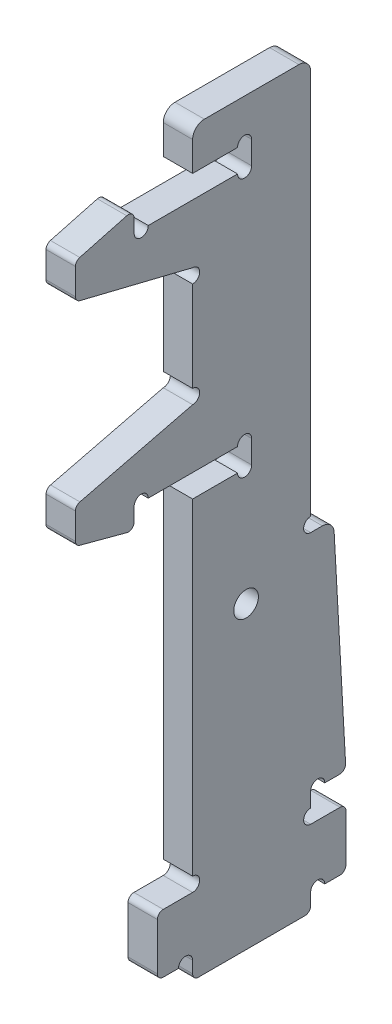
SolidWorks part; units mm, degrees
ref_plane "前视基准面" through (0, 0, 0) normal (0, 0, 1) x (1, 0, 0)
ref_plane "上视基准面" through (0, 0, 0) normal (0, 1, 0) x (1, 0, 0)
ref_plane "右视基准面" through (0, 0, 0) normal (1, 0, 0) x (0, 0, -1)
sketch "草图2" plane through (0, 0, 0) normal (1, 0, 0) x (0, 0, -1)
  line L0 (-5.025, 65) -> (-5.025, 8.5)
  line L1 (-5.025, 8.5) -> (-8.025, 8.5)
  line L2 (-8.025, 8.5) -> (-8.025, 3.5)
  line L3 (-8.025, 3.5) -> (-5.025, 3.5)
  line L4 (-5.025, 3.5) -> (-5.025, 2)
  line L5 (-5.025, 2) -> (5.025, 2)
  line L6 (5.025, 2) -> (5.025, 3.5)
  line L7 (5.025, 3.5) -> (8.025, 3.5)
  line L8 (8.025, 3.5) -> (8.025, 8.5)
  line L9 (8.025, 8.5) -> (5.025, 8.5)
  line L10 (5.025, 8.5) -> (5.025, 65)
  line L11 (5.025, 65) -> (-5.025, 65)
  line L12 (5.025, 0) -> (-5.025, 0) construction
  point P13 (-8.025, 6)
  point P19 (0, 0)
  dimension "D1" = 3
  dimension "D2" = 5
  dimension "D3" = 10.05
  dimension "D4" = 1.5
  dimension "D5" = 130
  dimension "D6" = 6
extrude "凸台-拉伸1" add sketch "草图2" along normal mid plane 2.5
sketch "草图4" plane through (-1.25, 0, 0) normal (-1, 0, 0) x (0, 0, 1)
  line L0 (-5.025, 65) -> (-8.025, 10.95)
  line L1 (-5.025, 8.5) -> (-5.025, 65) construction
  line L2 (-8.025, 10.95) -> (-5.025, 10.95)
  line L3 (-5.025, 10.95) -> (-5.025, 65)
  line L4 (-8.025, 8.5) -> (-5.025, 8.5) construction
  line L5 (-5.025, 65) -> (5.025, 65) construction
  line L6 (-8.025, 3.5) -> (-8.025, 8.5) construction
  dimension "D1" = 2.45
extrude "凸台-拉伸2" add sketch "草图4" against normal blind 2.5
sketch "草图3" plane through (1.25, 0, 0) normal (1, 0, 0) x (0, 0, -1)
  line L0 (-5.025, 65) -> (-5.025, 8.5) construction
  line L1 (-8.025, 3.5) -> (-5.025, 3.5) construction
  line L2 (5.025, 8.5) -> (5.025, 10.95) construction
  line L3 (5.025, 3.5) -> (8.025, 3.5) construction
  line L4 (8.025, 10.95) -> (5.025, 10.95) construction
  circle A0 centre (-5.025, 9.1) radius 0.6
  circle A1 centre (-5.625, 3.5) radius 0.6
  circle A2 centre (5.025, 9.1) radius 0.6
  circle A3 centre (5.625, 3.5) radius 0.6
  circle A4 centre (5.625, 10.95) radius 0.6
  dimension "D1" = 1.2
extrude "切除-拉伸1" cut sketch "草图3" against normal through all
fillet "圆角1" radius 0.5 7 edges at (0, 3.5, -8.025) (0, 8.5, -8.025) (0, 3.5, 8.025) (0, 8.5, 8.025) (0, 10.95, -8.025) (0, 2, 5.025) (0, 2, -5.025)
sketch "草图5" plane through (1.25, 0, 0) normal (1, 0, 0) x (0, 0, -1)
  line L0 (-5.025, 37.5) -> (0, 37.5)
  line L1 (-5.025, 65) -> (-5.025, 9.7) construction
  line L2 (0, 37.5) -> (0, 39.45)
  line L3 (0, 39.45) -> (-5.025, 39.45)
  line L4 (-5.025, 39.45) -> (-5.025, 37.5)
  line L5 (0, 65) -> (0, 61.5) construction
  line L6 (-5.025, 61.5) -> (0, 61.5)
  line L7 (-5.025, 61.5) -> (-5.025, 59.55)
  line L8 (-5.025, 59.55) -> (0, 59.55)
  line L9 (0, 61.5) -> (0, 59.55)
  line L10 (5.025, 65) -> (-5.025, 65) construction
  dimension "D2" = 1.95
  dimension "D3" = 37.5
  dimension "D4" = 24
extrude "切除-拉伸2" cut sketch "草图5" against normal through all
sketch "草图6" plane through (1.25, 0, 0) normal (1, 0, 0) x (0, 0, -1)
  line L0 (0, 61.5) -> (-5.025, 61.5) construction
  line L1 (-5.025, 59.55) -> (0, 59.55) construction
  line L2 (0, 39.45) -> (-5.025, 39.45) construction
  line L3 (-5.025, 37.5) -> (0, 37.5) construction
  circle A0 centre (-0.6, 61.5) radius 0.6
  circle A1 centre (-0.6, 59.55) radius 0.6
  circle A2 centre (-0.6, 39.45) radius 0.6
  circle A3 centre (-0.6, 37.5) radius 0.6
  dimension "D1" = 1.2
extrude "切除-拉伸3" cut sketch "草图6" against normal through all
sketch "草图7" plane through (-1.25, 0, 0) normal (-1, 0, 0) x (0, 0, 1)
  line L0 (-5.025, 65) -> (-5.025, 30)
  line L1 (-5.025, 30) -> (-6.9676, 30)
  line L2 (-5.025, 65) -> (-7.9957, 11.4777) construction
  line L3 (-6.9676, 30) -> (-5.025, 65)
  dimension "D1" = 30
extrude "切除-拉伸4" cut sketch "草图7" against normal through all
sketch "草图8" plane through (-1.25, 0, 0) normal (-1, 0, 0) x (0, 0, 1)
  line L0 (-5.025, 30) -> (-5.025, 65) construction
  circle A0 centre (-5.025, 30.6) radius 0.6
  arc A2 (0, 37.5) -> (1.2, 37.5) centre (0.6, 37.5) ccw construction
extrude "切除-拉伸5" cut sketch "草图8" against normal through all
fillet "圆角2" radius 1 3 edges at (0, 65, -5.025) (0, 65, 5.025) (0, 30, -6.9676)
sketch "草图9" plane through (-1.25, 0, 0) normal (-1, 0, 0) x (0, 0, 1)
  line L0 (5.025, 59.55) -> (10, 59.55)
  line L1 (10, 59.55) -> (10, 61.35)
  line L2 (10, 61.35) -> (15, 60.0103)
  line L3 (15, 60.0103) -> (15, 57.0103)
  line L4 (15, 57.0103) -> (5.025, 54.55)
  line L5 (5.025, 59.55) -> (5.025, 39.45) construction
  line L6 (5.025, 54.55) -> (5.025, 59.55)
  line L7 (5.025, 49.5) -> (15, 49.5) construction
  line L8 (15, 41.9897) -> (5.025, 44.45)
  line L9 (15, 38.9897) -> (15, 41.9897)
  line L10 (10, 37.65) -> (15, 38.9897)
  line L11 (10, 39.45) -> (10, 37.65)
  line L12 (5.025, 39.45) -> (10, 39.45)
  line L13 (5.025, 44.45) -> (5.025, 39.45)
  line L14 (0, 59.55) -> (0, 61.5) construction
  dimension "D1" = 1.8
  dimension "D2" = 5
  dimension "D3" = 5
  dimension "D4" = 10
  dimension "D5" = 75
  dimension "D6" = 3
extrude "凸台-拉伸3" add sketch "草图9" against normal blind 2.5
sketch "草图10" plane through (-1.25, 0, 0) normal (-1, 0, 0) x (0, 0, 1)
  line L0 (5.025, 54.55) -> (5.025, 44.45) construction
  line L2 (10, 59.55) -> (1.2, 59.55) construction
  line L3 (1.2, 39.45) -> (10, 39.45) construction
  circle A0 centre (5.025, 53.95) radius 0.6
  circle A1 centre (5.025, 45.05) radius 0.6
  circle A3 centre (9.4, 59.55) radius 0.6
  circle A4 centre (9.4, 39.45) radius 0.6
  arc A5 (0, 59.55) -> (1.2, 59.55) centre (0.6, 59.55) ccw construction
extrude "切除-拉伸6" cut sketch "草图10" against normal through all
fillet "圆角3" radius 0.5 6 edges at (0, 60.0103, 15) (0, 57.0103, 15) (0, 61.35, 10) (0, 37.65, 10) (0, 38.9897, 15) (0, 41.9897, 15)
sketch "草图11" plane through (1.25, 0, 0) normal (1, 0, 0) x (0, 0, -1)
  line L0 (5.025, 31.2) -> (5.025, 64) construction
  line L1 (6.0216, 30) -> (5.025, 30) construction
  circle A0 centre (-0.475, 27.5) radius 1.05
  dimension "D1" = 5.5
  dimension "D2" = 2.5
  dimension "D3" = 2.1
extrude "切除-拉伸7" cut sketch "草图11" against normal through all
